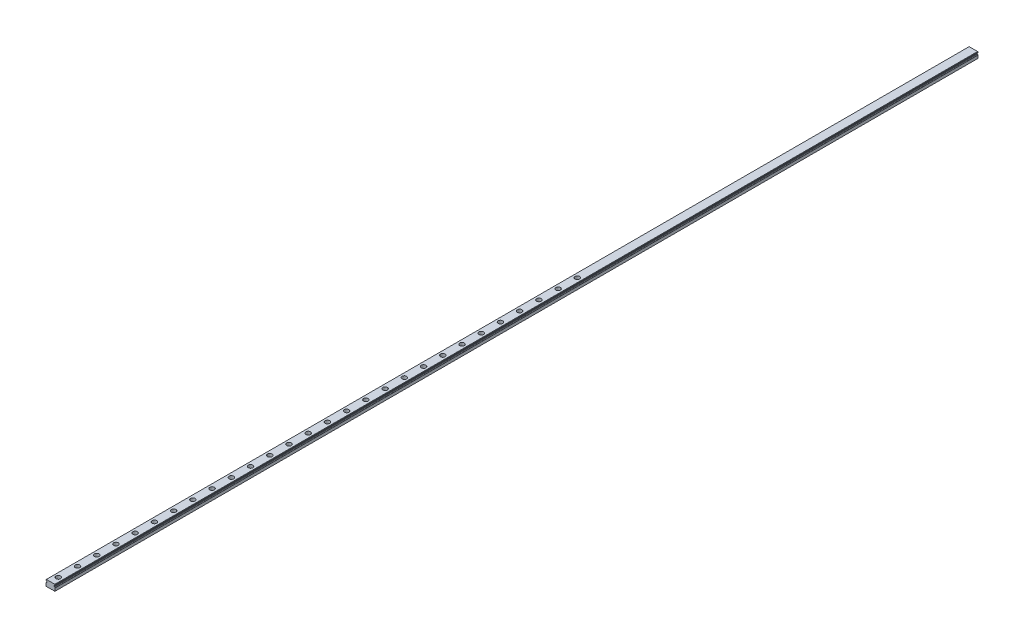
SolidWorks part; units mm, degrees
ref_plane "Front Plane" through (0, 0, 0) normal (0, 0, 1) x (1, 0, 0)
ref_plane "Top Plane" through (0, 0, 0) normal (0, 1, 0) x (1, 0, 0)
ref_plane "Right Plane" through (0, 0, 0) normal (1, 0, 0) x (0, 0, -1)
sketch "Sketch1" plane through (0, 0, 0) normal (0, 0, 1) x (1, 0, 0)
  line L0 (-6, 0) -> (6, 0) construction
  line L1 (0, -4) -> (0, 4) construction
  line L2 (0, 4) -> (0, -4) construction
  line L3 (-3, 4) -> (3, 4) construction
  line L4 (-1.75, -0.5) -> (1.75, -0.5) construction
  point P0 (0, -0.5)
  point P3 (-6, -4)
  point P4 (0, 0)
  point P8 (0, 0)
  point P11 (0, 4)
  point P15 (0, 4)
  point P17 (0, -0.5)
  point P18 (6, 4)
  point P20 (-6, 4)
  dimension "Rail Width" = 12
  dimension "Rail Height" = 8
  dimension "Mounting Hole Depth" = 3.5
  dimension "Mounting Hole Counterbore Diameter" = 6
  dimension "Mounting Hole Diameter" = 3.5
sketch "Sketch2" plane through (0, 0, 0) normal (1, 0, 0) x (0, 0, -1)
  line L0 (600, 0) -> (-600, 0) construction
  line L1 (-14, 4) -> (14, 4) construction
  line L3 (0, 4) -> (0, 0) construction
  point P0 (-590, 0)
  point P4 (0, 0)
  point P5 (-565, 0)
  point P6 (-577.5, 0)
  point P9 (-590, 4)
  point P10 (0, 4)
  point P11 (600, 4)
  point P13 (-600, 4)
  point P14 (577.5, 0)
  point P17 (-600, -4)
  dimension "Rail Length" = 1200
  dimension "Mounting Hole Center to Edge" = 10
  dimension "Mounting Hole Center to Center" = 25
  dimension "Number of Mounting Holes" = 28
  dimension "Break Line" = 12.5
sketch "Sketch3" plane through (0, 0, 0) normal (0, 0, 1) x (1, 0, 0)
  point P0 (0, 4)
  line B0 (-6, 0.1421) -> (-6, -3.5)
  line B1 (-6, -3.5) -> (-5.5, -4)
  line B2 (-5.5, -4) -> (1.6, -4)
  line B3 (2.4, -4) -> (5.5, -4)
  line B4 (5.5, -4) -> (6, -3.5)
  line B5 (6, -3.5) -> (6, 0.1421)
  line B6 (5.0738, 0.9945) -> (4.7282, 1.0247)
  line B7 (4.5, 1.2738) -> (4.5, 1.7262)
  line B8 (4.7282, 1.9753) -> (5.0948, 2.0073)
  line B9 (6, 2.8254) -> (6, 3.5)
  line B10 (6, 3.5) -> (5.5, 4)
  line B11 (5.5, 4) -> (-5.5, 4)
  line B12 (-5.5, 4) -> (-6, 3.5)
  line B13 (-6, 3.5) -> (-6, 2.8254)
  line B14 (-5.0948, 2.0073) -> (-4.7282, 1.9753)
  line B15 (-4.5, 1.7262) -> (-4.5, 1.2738)
  line B16 (-4.7282, 1.0247) -> (-5.0738, 0.9945)
  arc B17 (-5.8448, 0.3734) -> (-6, 0.1421) centre (-5.75, 0.1421) ccw
  arc B18 (2.4, -4) -> (1.6, -4) centre (2, -4.3) ccw
  arc B19 (6, 0.1421) -> (5.8448, 0.3734) centre (5.75, 0.1421) ccw
  arc B20 (5.2672, 0.8728) -> (5.8448, 0.3734) centre (6.3, 1.4838) ccw
  arc B21 (5.2672, 0.8728) -> (5.0738, 0.9945) centre (5.052, 0.7455) ccw
  arc B22 (4.5, 1.2738) -> (4.7282, 1.0247) centre (4.75, 1.2738) ccw
  arc B23 (4.7282, 1.9753) -> (4.5, 1.7262) centre (4.75, 1.7262) ccw
  arc B24 (5.0948, 2.0073) -> (5.2845, 2.1232) centre (5.073, 2.2564) ccw
  arc B25 (5.8448, 2.5941) -> (5.2845, 2.1232) centre (6.3, 1.4838) ccw
  arc B26 (5.8448, 2.5941) -> (6, 2.8254) centre (5.75, 2.8254) ccw
  arc B27 (-6, 2.8254) -> (-5.8448, 2.5941) centre (-5.75, 2.8254) ccw
  arc B28 (-5.2845, 2.1232) -> (-5.8448, 2.5941) centre (-6.3, 1.4838) ccw
  arc B29 (-5.2845, 2.1232) -> (-5.0948, 2.0073) centre (-5.073, 2.2564) ccw
  arc B30 (-4.5, 1.7262) -> (-4.7282, 1.9753) centre (-4.75, 1.7262) ccw
  arc B31 (-4.7282, 1.0247) -> (-4.5, 1.2738) centre (-4.75, 1.2738) ccw
  arc B32 (-5.0738, 0.9945) -> (-5.2672, 0.8728) centre (-5.052, 0.7455) ccw
  arc B33 (-5.8448, 0.3734) -> (-5.2672, 0.8728) centre (-6.3, 1.4838) ccw
sketch_block_instance "12mm Block-1"
sketch_block "12mm Block"
extrude "Boss-Extrude1" add sketch "Sketch3" against normal up to vertex (600 mm away) from vertex at 600 starting at point (0, 0, 600)
ref_plane "Plane1" through (0, 0, 590) normal (0, 0, 1) x (1, 0, 0)
sketch "Sketch4" plane through (0, 0, 590) normal (0, 0, 1) x (1, 0, 0)
  line L0 (0, 4) -> (0, -4)
  line L1 (0, -4) -> (-1.75, -4)
  line L3 (-1.75, -4) -> (-1.75, -0.5)
  line L4 (-1.75, -0.5) -> (-3, -0.5)
  line L5 (-3, -0.5) -> (-3, 4)
  line L6 (-3, 4) -> (0, 4)
revolve "Cut-Revolve1" cut sketch "Sketch4" angle 360 about L0
sketch "Sketch6" plane through (0, 0, 0) normal (1, 0, 0) x (0, 0, -1)
  line L0 (-587, -0.5) -> (-593, -0.5) construction
  line L5 (-587, -0.5) -> (-593, -0.5)
  line L17 (-591.75, -0.5) -> (-591.75, -4) construction
  line L18 (-588.25, -4) -> (-588.25, -0.5) construction
  line L32 (-587, -0.5) -> (-587, 4) construction
  line L33 (-593, 4) -> (-593, -0.5) construction
  line L34 (-591.75, -0.5) -> (-591.75, -4)
  line L35 (-588.25, -4) -> (-588.25, -0.5)
  line L36 (-587, -0.5) -> (-587, 4)
  line L37 (-593, 4) -> (-593, -0.5)
  line L38 (0, 4) -> (0, -4) construction
  line L40 (593, 4) -> (593, -0.5)
  line L41 (587, -0.5) -> (587, 4)
  line L42 (588.25, -4) -> (588.25, -0.5)
  line L43 (591.75, -0.5) -> (591.75, -4)
  line L44 (587, -0.5) -> (593, -0.5)
sketch "Sketch7" plane through (0, 0, 0) normal (0, 0, 1) x (1, 0, 0)
  line L0 (3, -0.5) -> (3, 4) construction
  line L1 (-3, 4) -> (-3, -0.5) construction
  line L2 (3, -0.5) -> (3, 4)
  line L3 (-3, 4) -> (-3, -0.5)
  line L4 (1.75, -3.867) -> (1.75, -0.5) construction
  line L11 (1.75, -3.867) -> (1.75, -0.5)
  line L18 (-1.75, -0.5) -> (-1.75, -4) construction
  line L32 (3, -0.5) -> (-3, -0.5) construction
  line L34 (-1.75, -0.5) -> (-1.75, -4)
  line L37 (3, -0.5) -> (-3, -0.5)
pattern_linear "LPattern1" count 28 spacing 25 along (0, 0, -1) of "Cut-Revolve1"
equation "\"D3@LPattern1\"=\"Mounting Hole Center to Center@Sketch2\""
equation "\"D1@LPattern1\"=\"Number of Mounting Holes@Sketch2\""
equation "\"Break Line@Sketch2\"=\"Mounting Hole Center to Center@Sketch2\"/2"
